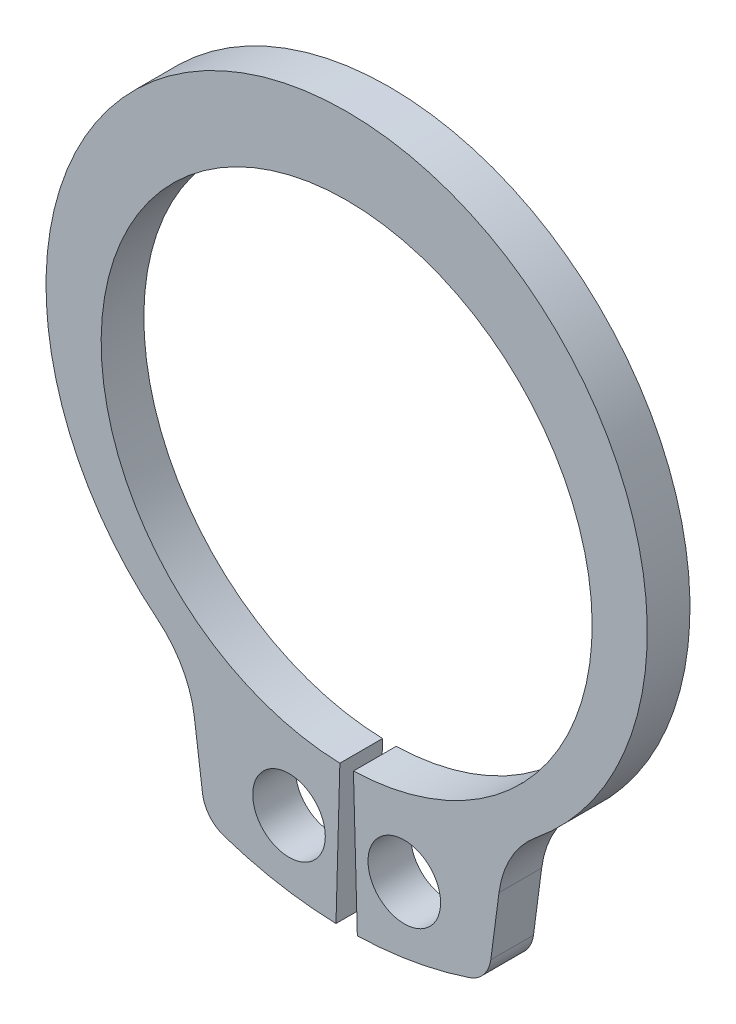
SolidWorks part; units mm, degrees
ref_plane "Plane1" through (0, 0, 0) normal (0, 0, 1) x (1, 0, 0)
ref_plane "Plane2" through (0, 0, 0) normal (0, 1, 0) x (1, 0, 0)
ref_plane "Plane3" through (0, 0, 0) normal (1, 0, 0) x (0, 0, -1)
extrude "Body" add sketch "BodySke" against normal blind 1
sketch "BodySke" plane through (0, 0, 0) normal (0, 0, 1) x (1, 0, 0)
  line L0 (-1.5431, 0) -> (1.5431, 0) construction
  line L1 (0, 0) -> (0, 7.55) construction
  line L2 (0.1588, -5.7478) -> (0.25, -9.0465)
  line L3 (-0.1588, -5.7478) -> (-0.25, -9.0465)
  line L4 (0, 0) -> (5.9454, -6.8231) construction
  line L5 (0, 0) -> (-5.9454, -6.8231) construction
  line L7 (3.5679, -6.5101) -> (3.3758, -7.9695)
  line L8 (-3.5679, -6.5101) -> (-3.3758, -7.9695)
  circle A0 centre (0, 0) radius 5.75 construction
  arc A1 (0.1588, -5.7478) -> (-0.1588, -5.7478) centre (0, 0) ccw
  arc A2 (4.3687, -5.0137) -> (-4.3687, -5.0137) centre (0, 0.5086) ccw construction
  arc A3 (0.25, -9.0465) -> (2.8701, -8.5828) centre (0, 0) ccw
  arc A4 (4.435, -4.9605) -> (3.5679, -6.5101) centre (5.9454, -6.8231) ccw
  arc A5 (-3.5679, -6.5101) -> (-4.435, -4.9605) centre (-5.9454, -6.8231) ccw
  arc A6 (-2.8701, -8.5828) -> (-0.25, -9.0465) centre (0, 0) ccw
  arc A7 (4.435, -4.9605) -> (-4.435, -4.9605) centre (0, 0.5086) ccw
  arc A8 (-3.5516, -6.6341) -> (3.5516, -6.6341) centre (0, 0) ccw construction
  circle A9 centre (1.35, -7.4029) radius 0.85
  circle A10 centre (-1.35, -7.4029) radius 0.85
  arc A11 (3.3758, -7.9695) -> (2.8701, -8.5828) centre (2.6322, -7.8716) cw
  arc A12 (-3.3758, -7.9695) -> (-2.8701, -8.5828) centre (-2.6322, -7.8716) ccw
  point P28 (3.3164, -8.4204)
  point P31 (-3.3164, -8.4204)
  dimension "GrooveDia" = 11.5
  dimension "D3" = 0.75
  dimension "LugRad" = 9.05
  dimension "HoleOffsetRad" = 7.525
  dimension "HoleDia" = 1.7
  dimension "D2" = 15
  dimension "LargeRad" = 7.55
  dimension "SmallRad" = 6.65
  dimension "Gap" = 0.5
  dimension "SmallAngle" = 82.135
  dimension "HoleSpacing" = 2.7
sketch "Clipboard" plane through (0, 0, 0) normal (0, 0, 1) x (1, 0, 0)
  line L0 (0, 0) -> (1.8, 0)
  line L1 (0, 0) -> (0, 0.9)
  line L2 (0, 0) -> (0, -3.3)
  circle A0 centre (0, 0) radius 0.85
  circle A1 centre (0, 0) radius 6
  dimension "HoleDia" = 1.7
  dimension "ShaftDia" = 12
  dimension "LargeSection" = 1.8
  dimension "SmallSection" = 0.9
  dimension "LugSection" = 3.3
sketch "NotSke" plane through (0, 0, 0) normal (0, 0, 1) x (1, 0, 0)
  line L0 (1.35, -6.5529) -> (1.35, -8.2529)
  line L1 (1.35, -8.2529) -> (-1.35, -8.2529)
  line L2 (-1.35, -8.2529) -> (-1.35, -6.5529)
  line L3 (-1.35, -6.5529) -> (1.35, -6.5529)
  circle A0 centre (1.35, -7.4029) radius 0.85 construction
  circle A1 centre (-1.35, -7.4029) radius 0.85 construction
extrude "Notch" [suppressed] cut sketch "NotSke" against normal through all
sketch "UnlSke" plane through (0, 0, 0) normal (0, 0, 1) x (1, 0, 0)
  line L0 (-2.6189, -8.6628) -> (-1.6639, -5.504)
  line L1 (2.6189, -8.6628) -> (1.6639, -5.504)
  arc A0 (1.6639, -5.504) -> (-1.6639, -5.504) centre (0, 0) ccw
  arc A1 (2.6189, -8.6628) -> (-2.6189, -8.6628) centre (0, 0) ccw
  arc A2 (0.25, -9.0465) -> (2.8701, -8.5828) centre (0, 0) ccw construction
  arc A3 (0.1588, -5.7478) -> (-0.1588, -5.7478) centre (0, 0) ccw construction
  circle A4 centre (-1.35, -7.4029) radius 0.85 construction
  circle A5 centre (1.35, -7.4029) radius 0.85 construction
extrude "Unlug" [suppressed] add sketch "UnlSke" against normal through all
equation "' \"ShaftDia@Clipboard\" = 3"
equation "' \"Thickness@Body\" = 0.4"
equation "' \"GrooveDia@BodySke\" = 2.8"
equation "' \"LugSection@Clipboard\" = 1.9"
equation "' \"LargeSection@Clipboard\" = 0.8"
equation "' \"HoleDia@Clipboard\" = 1.0"
equation "' \"ShaftDia@Clipboard\" = 10"
equation "' \"Thickness@Body\" = 1.0"
equation "' \"GrooveDia@BodySke\" = 9.6"
equation "' \"LugSection@Clipboard\" = 3.3"
equation "' \"LargeSection@Clipboard\" = 1.8"
equation "' \"HoleDia@Clipboard\" = 1.5"
equation "\"SmallSection@Clipboard\" = \"LargeSection@Clipboard\" * 0.5"
equation "\"Gap@BodySke\" =  \"Thickness@Body\" / 2"
equation "\"LargeRad@BodySke\" =  \"GrooveDia@BodySke\" / 2 +  \"LargeSection@Clipboard\""
equation "\"SmallRad@BodySke\" =  \"GrooveDia@BodySke\" / 2 +  \"SmallSection@Clipboard\""
equation "\"LugRad@BodySke\" = \"GrooveDia@BodySke\" / 2 + \"LugSection@Clipboard\""
equation "\"HoleOffsetRad@BodySke\" = (  \"ShaftDia@Clipboard\" / 2 + \"LugRad@BodySke\" ) / 2"
equation "\"HoleSpacing@BodySke\" = \"Gap@BodySke\"  * 2 +  \"HoleDia@Clipboard\""
equation "\"HoleDia@BodySke\" =  \"HoleDia@Clipboard\""
equation "\"SmallAngle@BodySke\" = atn(\"HoleSpacing@BodySke\" / 2 / sqr(\"HoleOffsetRad@BodySke\"  * \"HoleOffsetRad@BodySke\" - (\"HoleSpacing@BodySke\" / 2) * (\"HoleSpacing@BodySke\" / 2) ))  * 7 *  (\"LargeRad@BodySke\" / \"SmallRad@BodySke\")* ( 180 / 3.141593)"
